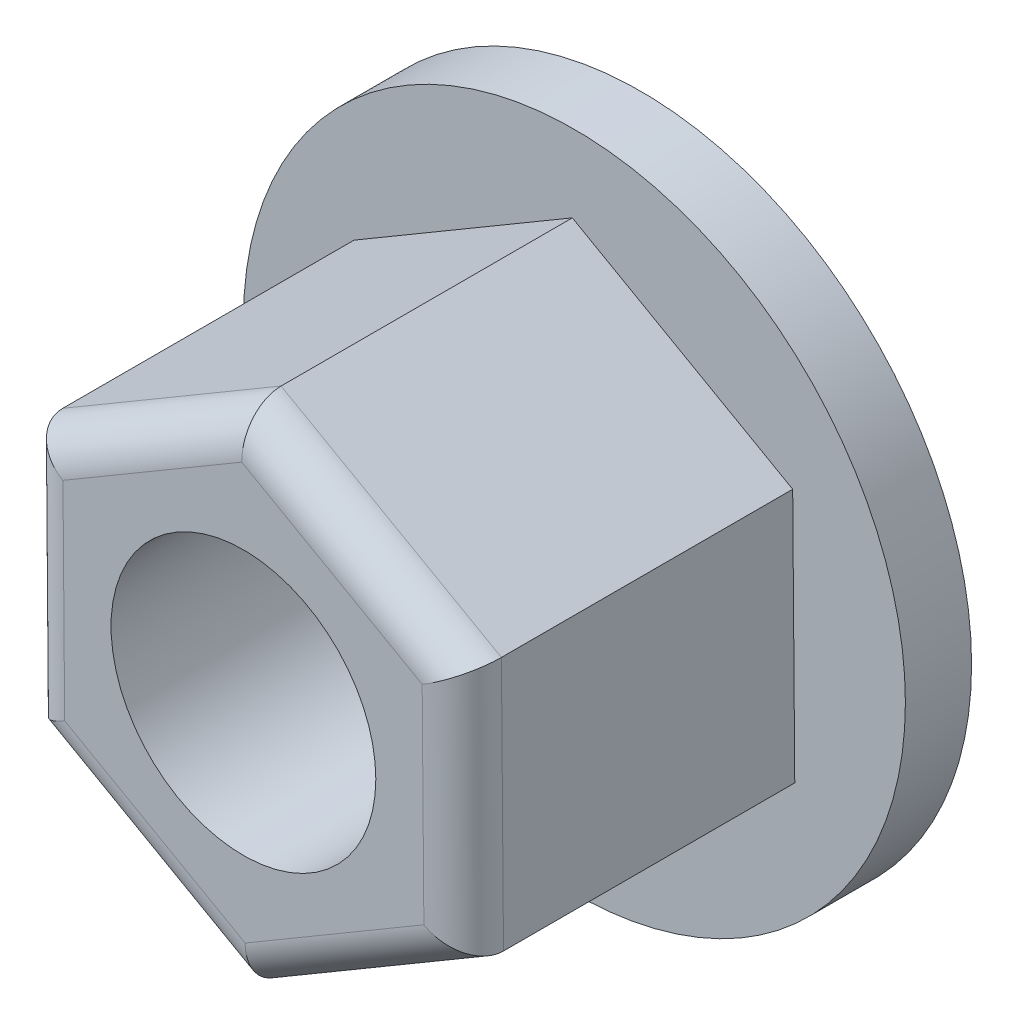
SolidWorks part; units mm, degrees
ref_plane "Front Plane" through (0, 0, 0) normal (0, 0, 1) x (1, 0, 0)
ref_plane "Top Plane" through (0, 0, 0) normal (0, 1, 0) x (1, 0, 0)
ref_plane "Right Plane" through (0, 0, 0) normal (1, 0, 0) x (0, 0, -1)
sketch "Sketch2" plane through (0, 0, 0) normal (0, 0, 1) x (1, 0, 0)
  circle A0 centre (0, 0) radius 25
  dimension "D1" = 50
extrude "Boss-Extrude1" add sketch "Sketch2" along normal blind 5
sketch "Sketch3" plane through (0, 0, 5) normal (0, 0, 1) x (1, 0, 0)
  line L1 (16.6444, -9.4279) -> (16.487, 9.7005)
  line L2 (16.487, 9.7005) -> (-0.1574, 19.1284)
  line L3 (-0.1574, 19.1284) -> (-16.6444, 9.4279)
  line L4 (-16.6444, 9.4279) -> (-16.487, -9.7005)
  line L5 (-16.487, -9.7005) -> (0.1574, -19.1284)
  line L6 (0.1574, -19.1284) -> (16.6444, -9.4279)
  circle A0 centre (0, 0) radius 16.5663 construction
extrude "Boss-Extrude2" add sketch "Sketch3" along normal blind 25
fillet "Fillet6" radius 3 6 edges at (-8.1648, -14.4145, 30) (-16.5657, -0.1363, 30) (-8.4009, 14.2782, 30) (8.1648, 14.4145, 30) (16.5657, 0.1363, 30) (8.4009, -14.2782, 30)
sketch "Sketch5" plane through (0, 0, 30) normal (0, 0, 1) x (1, 0, 0)
  circle A0 centre (0, 0) radius 10
  dimension "D1" = 20
extrude "Cut-Extrude1" cut sketch "Sketch5" against normal through all
